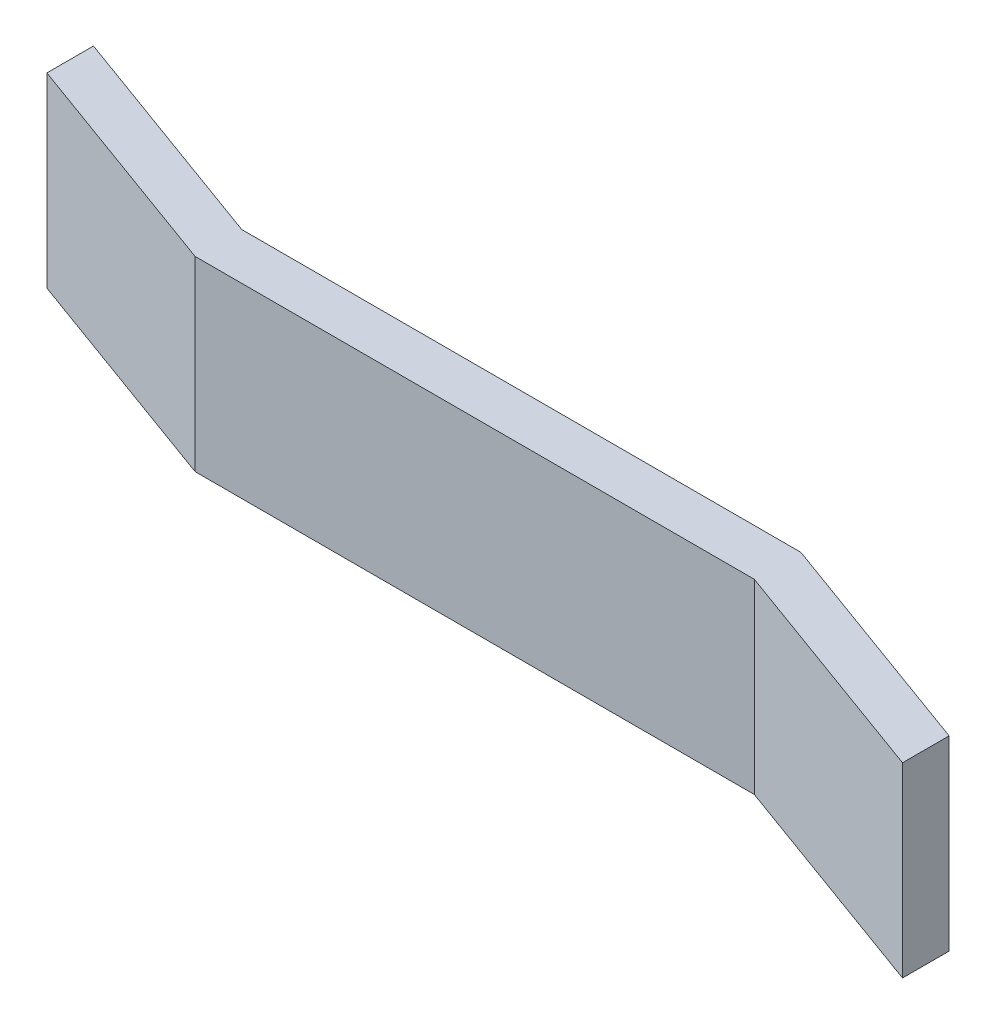
SolidWorks part; units mm, degrees
ref_plane "前视基准面" through (0, 0, 0) normal (0, 0, 1) x (1, 0, 0)
ref_plane "上视基准面" through (0, 0, 0) normal (0, 1, 0) x (1, 0, 0)
ref_plane "右视基准面" through (0, 0, 0) normal (1, 0, 0) x (0, 0, -1)
sketch "草图1" plane through (0, 0, 0) normal (0, 1, 0) x (1, 0, 0)
  line L0 (0, 0) -> (0, 5)
  line L1 (0, 0) -> (60, 0)
  line L2 (0, 0) -> (0, 5)
  line L3 (0, 5) -> (60, 5)
  line L4 (60, 0) -> (60, 5)
  line L5 (0, 0) -> (60, 5) construction
  line L6 (0, 5) -> (60, 0) construction
  line L7 (0, 0) -> (-25, 9.0993)
  line L8 (0, 5) -> (-25, 14.0993)
  line L9 (-25, 9.0993) -> (-25, 14.0993)
  line L10 (60, 0) -> (60, 5)
  line L11 (60, 0) -> (85, -9.0993)
  line L12 (60, 5) -> (85, -4.0993)
  line L13 (85, -9.0993) -> (85, -4.0993)
  point P4 (30, 2.5)
  dimension "D1" = 5
  dimension "D2" = 160
  dimension "D3" = 160
  dimension "D4" = 60
  dimension "D5" = 25
  dimension "D6" = 25
extrude "凸台-拉伸1" add sketch "草图1" along normal blind 20 contours L9 L7 L0 L8 | L1 L4 L3 L0 | L11 L13 L12 L4
